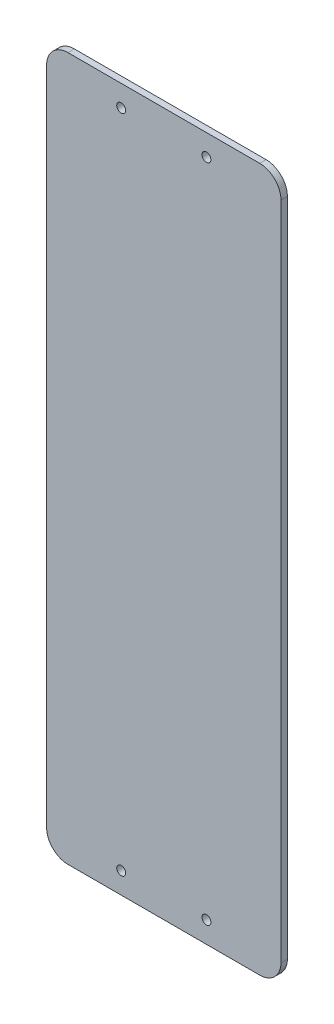
SolidWorks part; units mm, degrees
material "Balsa"
ref_plane "前视基准面" through (0, 0, 0) normal (0, 0, 1) x (1, 0, 0)
ref_plane "上视基准面" through (0, 0, 0) normal (0, 1, 0) x (1, 0, 0)
ref_plane "右视基准面" through (0, 0, 0) normal (1, 0, 0) x (0, 0, -1)
other "Configuration Table"
sketch "Sketch1" plane through (0, 0, 0) normal (0, 0, 1) x (1, 0, 0)
  line L0 (55, 330) -> (55, 0) construction
  line L1 (0, 0) -> (110, 0)
  line L2 (0, 0) -> (0, 330)
  line L3 (0, 330) -> (110, 330)
  line L4 (110, 0) -> (110, 330)
  line L5 (0, 165) -> (110, 165) construction
  circle A0 centre (35, 320) radius 2.1
  circle A4 centre (75, 320) radius 2.1
  circle A5 centre (75, 10) radius 2.1
  circle A6 centre (35, 10) radius 2.1
  dimension "D3" = 4.2
  dimension "D4" = 40
  dimension "D1" = 110
  dimension "D2" = 330
  dimension "D5" = 310
extrude "Boss-Extrude1" add sketch "Sketch1" along normal blind 3
fillet "Fillet1" radius 10 4 edges at (0, 330, 1.5) (0, 0, 1.5) (110, 330, 1.5) (110, 0, 1.5)
